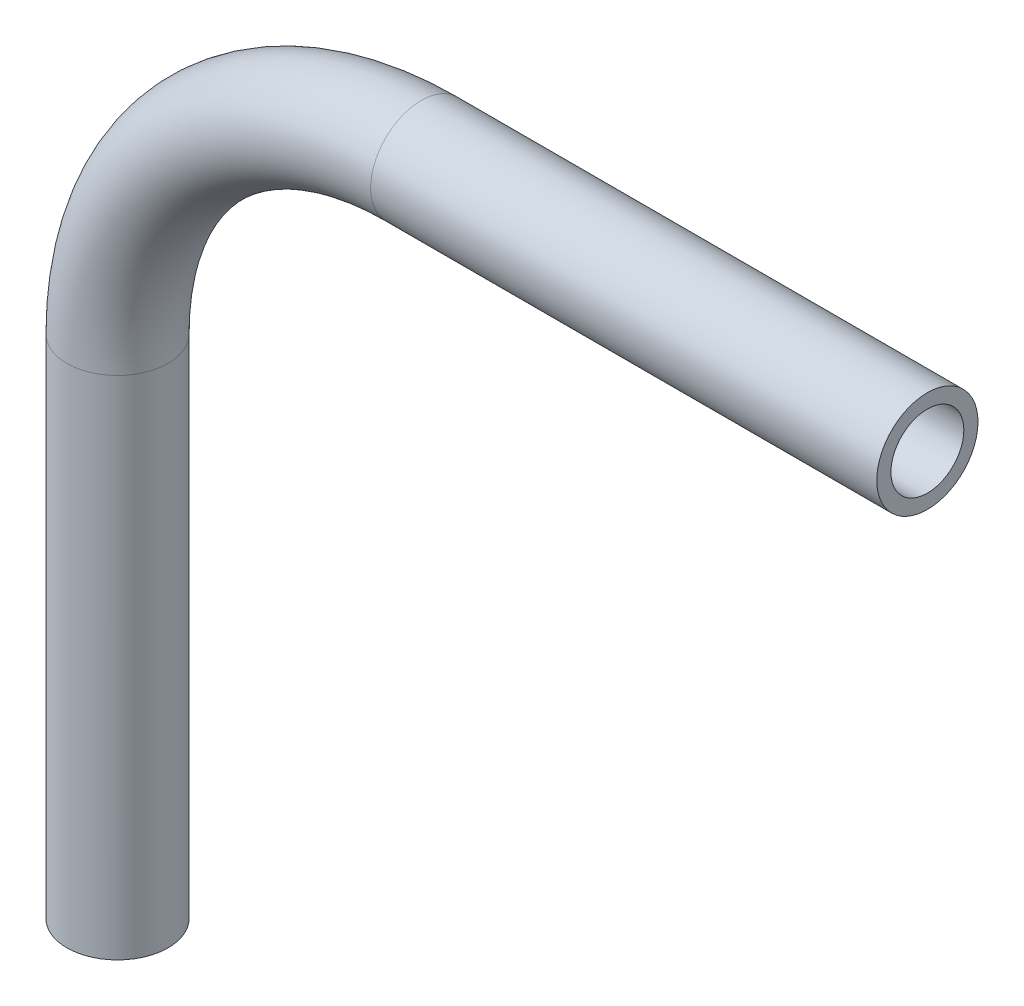
SolidWorks part; units mm, degrees
material "AISI 316 Stainless Steel Sheet (SS)"
ref_plane "Front Plane" through (0, 0, 0) normal (0, 0, 1) x (1, 0, 0)
ref_plane "Top Plane" through (0, 0, 0) normal (0, 1, 0) x (1, 0, 0)
ref_plane "Right Plane" through (0, 0, 0) normal (1, 0, 0) x (0, 0, -1)
sketch "Sketch1" plane through (0, 0, 0) normal (0, 0, 1) x (1, 0, 0)
  line L0 (0, -33.2723) -> (0, -1.5223)
  line L1 (19.05, 17.5277) -> (50.8, 17.5277)
  arc A0 (0, -1.5223) -> (19.05, 17.5277) centre (19.05, -1.5223) cw
  point P6 (0, 17.5277)
  dimension "D3" = 19.05
  dimension "D4" = 90
  dimension "D1" = 50.8
  dimension "D2" = 50.8
ref_plane "Plane1" through (50.8, 17.5277, 0) normal (1, 0, 0) x (0, 0, -1)
sketch "Sketch2" plane through (50.8, 17.5277, 0) normal (1, 0, 0) x (0, 0, -1)
  circle A0 centre (0, 0) radius 3.175
  circle A1 centre (0, 0) radius 2.286
  dimension "D1" = 6.35
  dimension "D2" = 4.572
sweep "Sweep1" add profiles "Sketch2" path "Sketch1"
